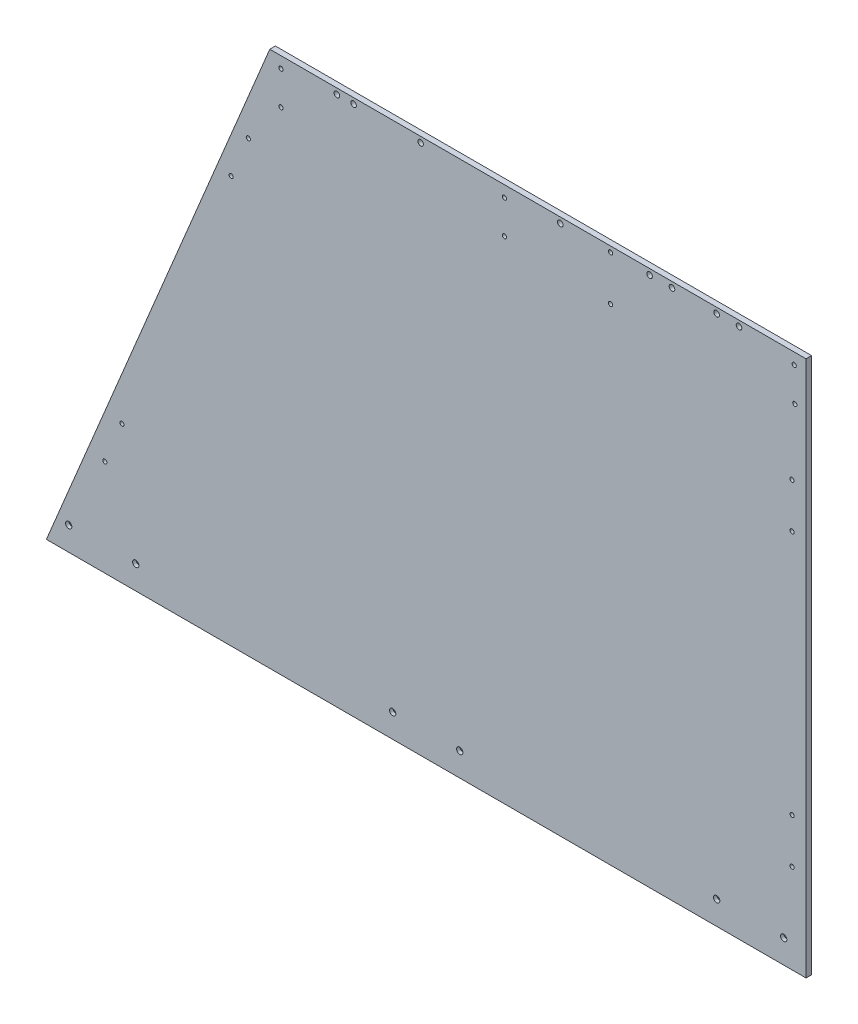
SolidWorks part; units mm, degrees
material "PC High Viscosity"
ref_plane "Front Plane" through (0, 0, 0) normal (0, 0, 1) x (1, 0, 0)
ref_plane "Top Plane" through (0, 0, 0) normal (0, 1, 0) x (1, 0, 0)
ref_plane "Right Plane" through (0, 0, 0) normal (1, 0, 0) x (0, 0, -1)
sketch "Sketch1" plane through (0, 0, 0) normal (0, 0, 1) x (1, 0, 0)
  line L0 (0, 0) -> (0, -609.6)
  line L1 (0, -609.6) -> (-863.6, -609.6)
  line L2 (-863.6, -609.6) -> (-609.6, 0)
  line L3 (-609.6, 0) -> (0, 0)
  dimension "D1" = 863.6
  dimension "D2" = 609.6
extrude "Boss-Extrude1" add sketch "Sketch1" against normal blind 6.35
sketch "Sketch2" plane through (0, 0, -6.35) normal (0, 0, -1) x (-1, 0, 0)
  line L0 (0, -609.6) -> (0, 0) construction
  line L1 (0, 0) -> (609.6, 0) construction
  line L2 (0, 0) -> (609.6, 0) construction
  line L3 (0, -609.6) -> (0, 0) construction
  line L4 (863.6, -609.6) -> (0, -609.6) construction
  line L5 (609.6, 0) -> (863.6, -609.6) construction
  line L6 (469.9, -582.7179) -> (393.7, -582.7179) construction
  circle A0 centre (342.9, -50.8) radius 2.413
  circle A1 centre (342.9, -12.7) radius 2.413
  circle A2 centre (596.9, -12.7) radius 2.413
  circle A3 centre (596.9, -50.8) radius 2.413
  circle A4 centre (13.462, -12.7) radius 2.413
  circle A5 centre (12.7, -50.8) radius 2.413
  circle A6 centre (15.875, -127.0214) radius 2.3813
  circle A7 centre (15.875, -177.8214) radius 2.3813
  circle A8 centre (15.875, -457.1023) radius 2.3813
  circle A9 centre (15.875, -507.9023) radius 2.3813
  circle A10 centre (101.6, -582.7179) radius 3.175
  circle A11 centre (25.4, -582.7179) radius 3.175
  circle A12 centre (762, -582.7179) radius 3.175
  circle A13 centre (838.2, -582.7179) radius 3.175
  circle A14 centre (797.1197, -499.5773) radius 2.3812
  circle A15 centre (777.5812, -452.685) radius 2.3812
  circle A16 centre (653.5679, -146.798) radius 2.3812
  circle A17 centre (634.0231, -99.8904) radius 2.3812
  circle A18 centre (514.35, -6.35) radius 3.133
  circle A19 centre (438.15, -6.35) radius 3.133
  circle A20 centre (469.9, -582.7179) radius 3.175
  circle A21 centre (393.7, -582.7179) radius 3.175
  point P53 (431.8, -582.7179)
  dimension "D8" = 4.826
  dimension "D14" = 4.7625
  dimension "D15" = 25.4
  dimension "D16" = 6.35
  dimension "D22" = 4.7625
  dimension "D34" = 6.2659
  dimension "D25" = 50.8165
  dimension "D26" = 26.8821
  dimension "D12" = 6.35
  dimension "D36" = 15.875
  dimension "D38" = 101.6977
  dimension "D1" = 330.2
  dimension "D2" = 15.875
  dimension "D3" = 12.7
  dimension "D4" = 38.1
  dimension "D5" = 38.1
  dimension "D6" = 254
  dimension "D7" = 12.7
  dimension "D9" = 127.0214
  dimension "D10" = 50.8
  dimension "D11" = 15.875
  dimension "D13" = 76.2
  dimension "D17" = 76.2
  dimension "D18" = 660.4
  dimension "D19" = 76.2
  dimension "D20" = 26.8821
  dimension "D21" = 50.8
  dimension "D23" = 15.875
  dimension "D24" = 110.0227
  dimension "D27" = 15.875
  dimension "D28" = 431.8
  dimension "D29" = 19.05
  dimension "D30" = 6.35
  dimension "D31" = 6.35
  dimension "D32" = 76.2
  dimension "D33" = 95.25
  dimension "D35" = 19.05
  dimension "D37" = 50.8
  dimension "D39" = 99.8904
extrude "Cut-Extrude1" cut sketch "Sketch2" against normal through all
sketch "Sketch3" plane through (0, 0, 0) normal (0, 0, 1) x (1, 0, 0)
  line L0 (0, 0) -> (-609.6, 0) construction
  line L1 (0, -609.6) -> (0, 0) construction
  circle A0 centre (-177.8, -6.35) radius 3.175
  circle A1 centre (-152.4, -6.35) radius 3.175
  circle A2 centre (-101.6, -6.35) radius 3.175
  circle A3 centre (-76.2, -6.35) radius 3.175
  dimension "D2" = 6.35
  dimension "D1" = 6.35
  dimension "D3" = 25.4
  dimension "D4" = 50.8
  dimension "D5" = 25.4
  dimension "D6" = 76.2
extrude "Cut-Extrude2" cut sketch "Sketch3" against normal blind 6.35
sketch "Sketch4" plane through (0, 0, -6.35) normal (0, 0, -1) x (-1, 0, 0)
  line L0 (0, 0) -> (609.6, 0) construction
  circle A0 centre (533.4, -6.35) radius 3.175
  circle A1 centre (279.4, -6.35) radius 3.175
  circle A2 centre (222.25, -6.35) radius 2.413
  circle A3 centre (222.25, -57.15) radius 2.413
  point P11 (0, 0)
  point P12 (0, 0)
  point P13 (0, 0)
  point P14 (0, 0)
  dimension "D1" = 76.2
  dimension "D3" = 6.35
  dimension "D4" = 6.35
  dimension "D6" = 4.826
  dimension "D2" = 254
  dimension "D5" = 6.35
  dimension "D7" = 50.8
  dimension "D8" = 57.15
extrude "Cut-Extrude3" cut sketch "Sketch4" against normal blind 6.35
hole_wizard "CSK for 1/4 Flat Head Machine Screw (100)1" positions "3DSketch1" profile "Sketch5" countersink size "1/4" standard "ANSI Inch" end condition through all
sketch3d "3DSketch1"
  line L0 (-25.4, -582.7179, 0) -> (-25.4, -582.7179, -6.35) construction
  line L1 (-101.6, -582.7179, 0) -> (-101.6, -582.7179, -6.35) construction
  line L2 (-393.7, -582.7179, 0) -> (-393.7, -582.7179, -6.35) construction
  line L3 (-469.9, -582.7179, 0) -> (-469.9, -582.7179, -6.35) construction
  line L4 (-762, -582.7179, 0) -> (-762, -582.7179, -6.35) construction
  line L5 (-838.2, -582.7179, 0) -> (-838.2, -582.7179, -6.35) construction
  point P28 (-25.4, -582.7179, -6.35)
  point P32 (-101.6, -582.7179, -6.35)
  point P36 (-393.7, -582.7179, -6.35)
  point P40 (-469.9, -582.7179, -6.35)
  point P44 (-762, -582.7179, -6.35)
  point P48 (-838.2, -582.7179, -6.35)
sketch "Sketch5" plane through (-25.4, -582.7179, -6.35) normal (1, 0, 0) x (0, 1, 0)
  line L0 (0, 0) -> (0, 6.35)
  line L1 (0, 6.35) -> (3.5712, 6.35)
  line L2 (3.5712, 6.35) -> (3.5712, 2.4063)
  line L3 (3.5712, 2.4063) -> (6.4389, 0)
  line L5 (6.4389, 0) -> (0, 0)
  line L6 (-3.5712, 2.4063) -> (-6.4389, 0) construction
  line L11 (0, -6.35) -> (0, 107.95) construction
  dimension "Thru Hole Dia." = 7.1425
  dimension "Thru Hole Depth" = 6.35
  dimension "Near C'Sink Dia." = 12.8778
  dimension "Near C'Sink Angle" = 100
